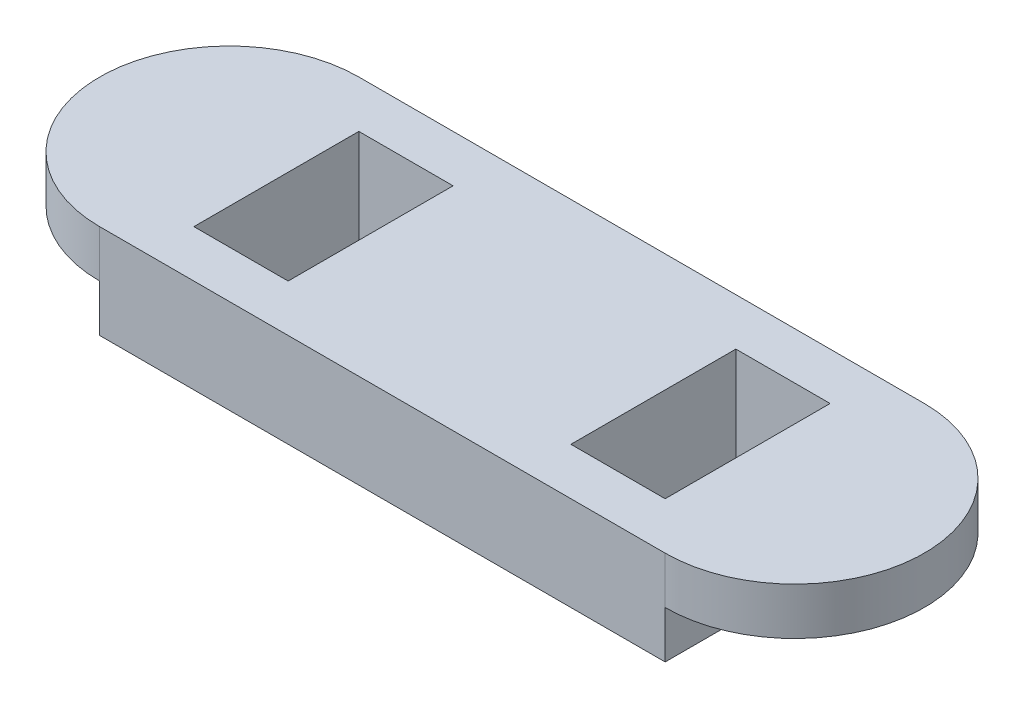
SolidWorks part; units mm, degrees
ref_plane "Front Plane" through (0, 0, 0) normal (0, 0, 1) x (1, 0, 0)
ref_plane "Top Plane" through (0, 0, 0) normal (0, 1, 0) x (1, 0, 0)
ref_plane "Right Plane" through (0, 0, 0) normal (1, 0, 0) x (0, 0, -1)
sketch "Sketch2" plane through (0, 0, 0) normal (0, 1, 0) x (1, 0, 0)
  line L1 (-60, -27.5) -> (60, -27.5)
  line L2 (-60, -27.5) -> (-60, 27.5)
  line L3 (-60, 27.5) -> (60, 27.5)
  line L4 (60, -27.5) -> (60, 27.5)
  line L5 (-60, -27.5) -> (60, 27.5) construction
  line L6 (-60, 27.5) -> (60, -27.5) construction
  point P0 (0, 0)
  dimension "D1" = 120
  dimension "D2" = 55
extrude "Boss-Extrude1" add sketch "Sketch2" along normal blind 20
sketch "Sketch3" plane through (0, 0, 0) normal (0, -1, 0) x (-1, 0, 0)
  line L0 (60, 27.5) -> (60, -27.5) construction
  line L1 (50, 17.5) -> (-50, 17.5)
  line L2 (50, 17.5) -> (50, -17.5)
  line L3 (50, -17.5) -> (-50, -17.5)
  line L4 (-50, 17.5) -> (-50, -17.5)
  line L5 (50, 17.5) -> (-50, -17.5) construction
  line L6 (50, -17.5) -> (-50, 17.5) construction
  line L8 (60, -27.5) -> (-60, -27.5) construction
  line L9 (0, 11) -> (0, -11) construction
  line L10 (50, -17.5) -> (30, -17.5)
  line L11 (50, -17.5) -> (50, 17.5)
  line L12 (50, 17.5) -> (30, 17.5)
  line L13 (30, -17.5) -> (30, 17.5)
  line L14 (-30, -17.5) -> (-30, 17.5)
  point P0 (0, 0)
  dimension "D1" = 10
  dimension "D2" = 10
  dimension "D3" = 20
extrude "Cut-Extrude1" cut sketch "Sketch3" against normal blind 20 contours L13 L3 L2 L1 | L3 L14 L1 L4
sketch "Sketch4" plane through (0, 20, 0) normal (0, 1, 0) x (1, 0, 0)
  line L0 (-60, 27.5) -> (-60, -27.5) construction
  line L1 (-60, -27.5) -> (-60, 27.5)
  line L2 (0, -11) -> (0, 11) construction
  arc A0 (-60, 27.5) -> (-60, -27.5) centre (-60, 0) ccw
  arc A1 (60, 27.5) -> (60, -27.5) centre (60, 0) cw
  point P8 (-60, 0)
  line M6 (60, -27.5) -> (60, 27.5)
  line M8 (-60, 27.5) -> (-60, -27.5)
extrude "Boss-Extrude2" add sketch "Sketch4" against normal blind 10 contours A0 M8 | A1 M6
